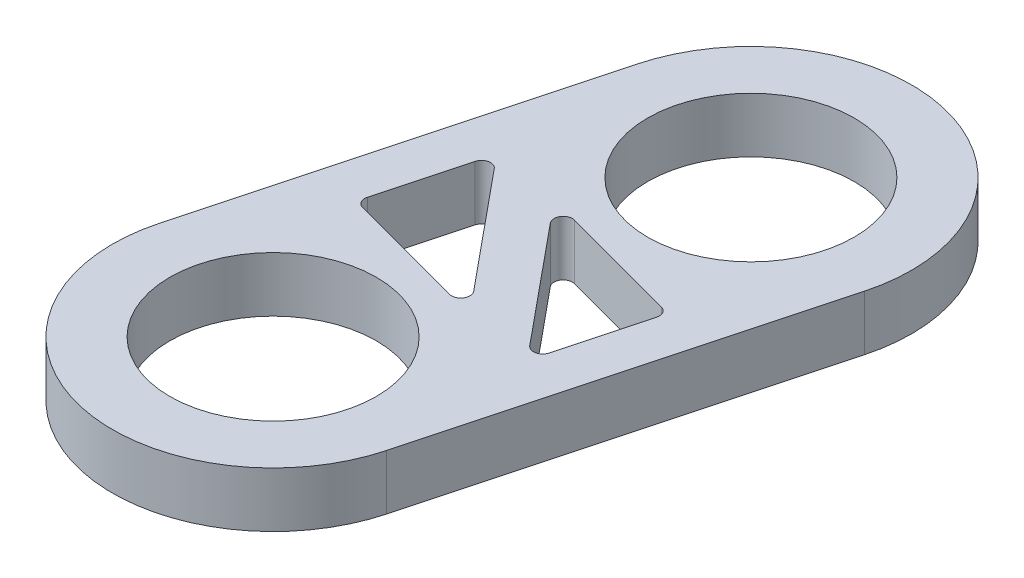
SolidWorks part; units mm, degrees
ref_plane "Front Plane" through (0, 0, 0) normal (0, 0, 1) x (1, 0, 0)
ref_plane "Top Plane" through (0, 0, 0) normal (0, 1, 0) x (1, 0, 0)
ref_plane "Right Plane" through (0, 0, 0) normal (1, 0, 0) x (0, 0, -1)
sketch "Sketch1" plane through (0, 0, 0) normal (0, 1, 0) x (1, 0, 0)
  line L0 (7.4979, -57.8881) -> (21.4677, -5.7523)
  line L1 (-35.4375, -46.3836) -> (-21.4677, 5.7523)
  line L2 (0, 0) -> (-13.9698, -52.1358) construction
  line L3 (0, -52.1358) -> (0, 0) construction
  circle A0 centre (0, 0) radius 23.8125 construction
  circle A1 centre (-13.9698, -52.1358) radius 23.8125 construction
  circle A2 centre (-13.9698, -52.1358) radius 14.2875
  circle A3 centre (0, 0) radius 14.2875
  arc A4 (-35.4375, -46.3836) -> (7.4979, -57.8881) centre (-13.9698, -52.1358) ccw
  arc A5 (21.4677, -5.7523) -> (0, 22.225) centre (0, 0) ccw
  circle A6 centre (-13.9698, -52.1358) radius 22.225 construction
  circle A8 centre (0, 0) radius 22.225 construction
  arc A9 (-21.4677, 5.7523) -> (0, 22.225) centre (0, 0) cw
  dimension "D1" = 47.625
  dimension "D2" = 28.575
  dimension "D3" = 28.575
  dimension "D4" = 44.45
  dimension "D5" = 53.975
  dimension "D6" = 15
extrude "Boss-Extrude1" add sketch "Sketch1" along normal blind 7.62
sketch "Sketch2" plane through (0, 7.62, 0) normal (0, 1, 0) x (1, 0, 0)
  line L0 (-28.4526, -20.3157) -> (14.4828, -31.8202) construction
  line L1 (-21.4677, 5.7523) -> (-35.4375, -46.3836) construction
  line L2 (7.4979, -57.8881) -> (21.4677, -5.7523) construction
  line L3 (-20.394, -14.7751) -> (-3.035, -35.8614)
  line L4 (-3.035, -35.8614) -> (-24.5027, -30.1092)
  line L5 (-24.5027, -30.1092) -> (-20.394, -14.7751)
  line L6 (-10.9347, -16.2744) -> (10.533, -22.0267)
  line L7 (10.533, -22.0267) -> (6.4242, -37.3608)
  line L8 (6.4242, -37.3608) -> (-10.9347, -16.2744)
  dimension "D1" = 6.35
  dimension "D2" = 22.225
  dimension "D3" = 15.875
  dimension "D4" = 6.35
  dimension "D5" = 6.35
extrude "Cut-Extrude1" cut sketch "Sketch2" against normal through all
fillet "Fillet1" radius 1.27 6 edges at (6.4242, 3.81, 37.3608) (10.533, 3.81, 22.0267) (-10.9347, 3.81, 16.2744) (-20.394, 3.81, 14.7751) (-24.5027, 3.81, 30.1092) (-3.035, 3.81, 35.8614)
